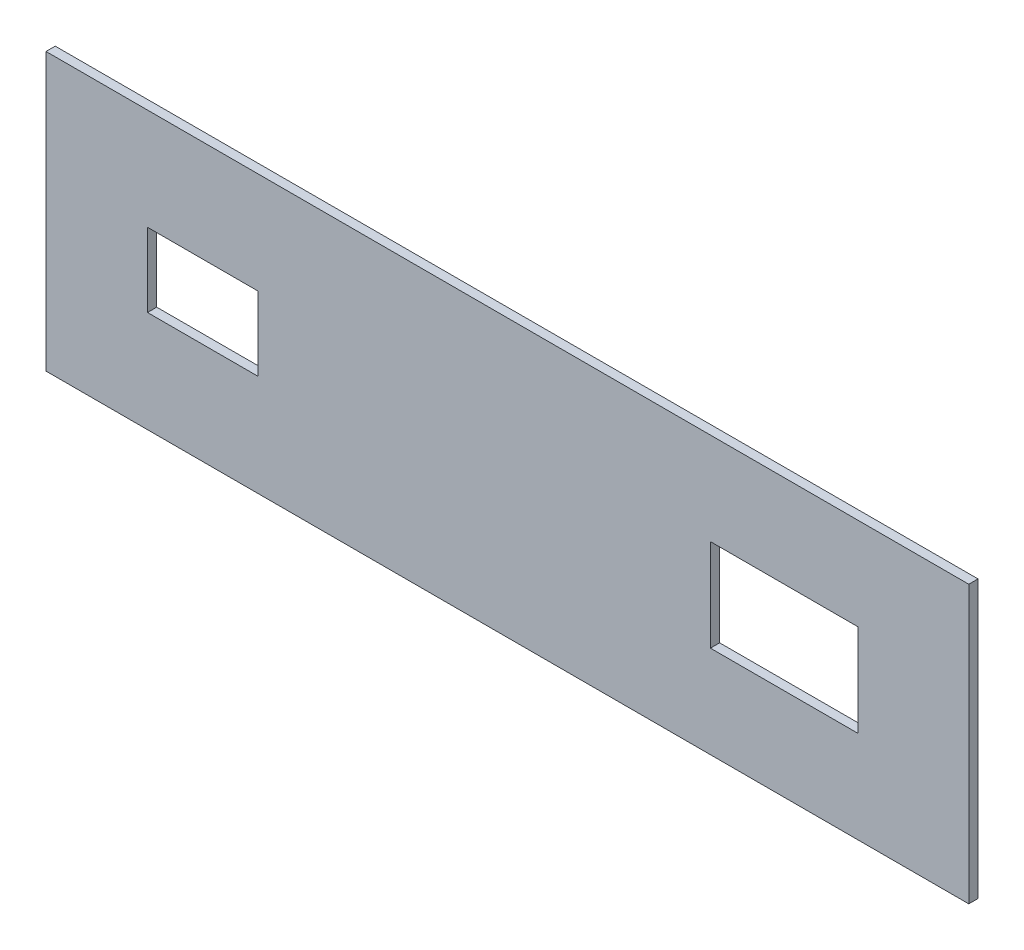
SolidWorks part; units mm, degrees
ref_plane "Front Plane" through (0, 0, 0) normal (0, 0, 1) x (1, 0, 0)
ref_plane "Top Plane" through (0, 0, 0) normal (0, 1, 0) x (1, 0, 0)
ref_plane "Right Plane" through (0, 0, 0) normal (1, 0, 0) x (0, 0, -1)
sketch "Sketch1" plane through (0, 0, 0) normal (0, 0, 1) x (1, 0, 0)
  line L0 (-80, 75) -> (-80, -75) construction
  line L1 (-250, 75) -> (250, 75)
  line L2 (-250, 75) -> (-250, -75)
  line L3 (-250, -75) -> (250, -75)
  line L4 (250, 75) -> (250, -75)
  line L5 (-250, 75) -> (250, -75) construction
  line L6 (-250, -75) -> (250, 75) construction
  line L7 (-195, 20) -> (-135, 20)
  line L8 (-195, 20) -> (-195, -20)
  line L9 (-195, -20) -> (-135, -20)
  line L10 (-135, 20) -> (-135, -20)
  line L11 (-195, 20) -> (-135, -20) construction
  line L12 (-195, -20) -> (-135, 20) construction
  line L14 (110, 25) -> (190, 25)
  line L15 (110, 25) -> (110, -25)
  line L16 (110, -25) -> (190, -25)
  line L17 (190, 25) -> (190, -25)
  line L18 (110, 25) -> (190, -25) construction
  line L19 (110, -25) -> (190, 25) construction
  point P0 (0, 0)
  point P6 (-165, 0)
  point P15 (150, 0)
  dimension "D1" = 500
  dimension "D2" = 150
  dimension "D3" = 60
  dimension "D4" = 170
  dimension "D5" = 40
  dimension "D6" = 75
  dimension "D7" = 85
  dimension "D8" = 100
  dimension "D9" = 80
  dimension "D10" = 50
extrude "Boss-Extrude1" add sketch "Sketch1" along normal blind 5
